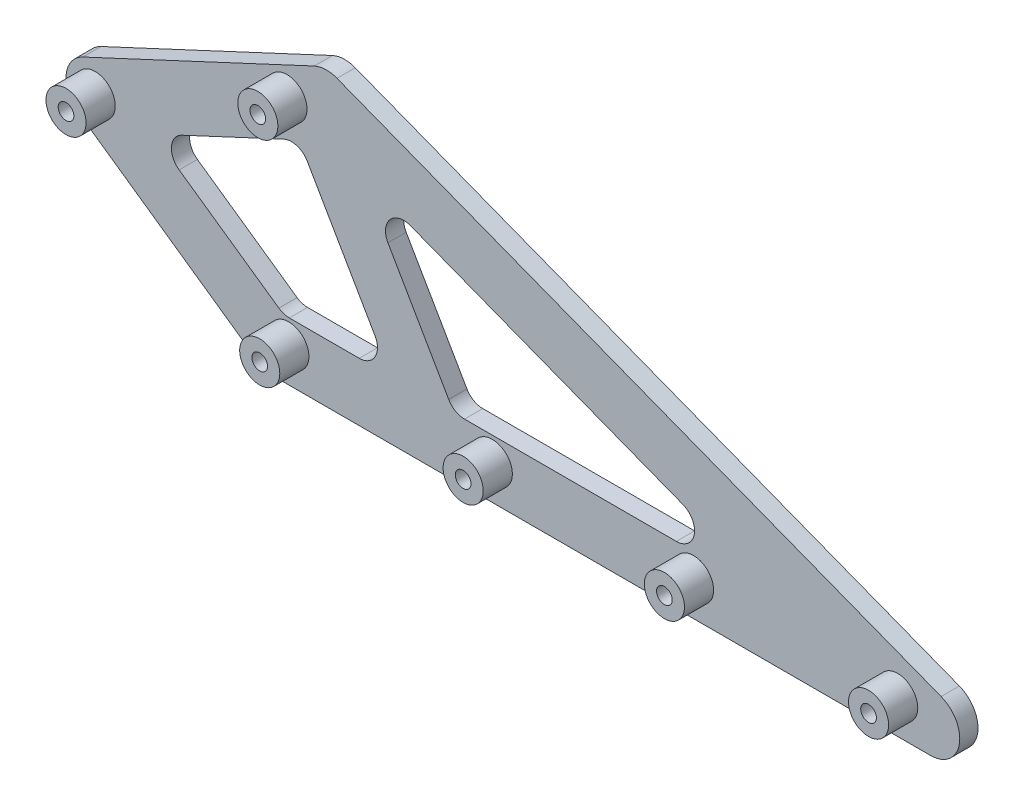
SolidWorks part; units mm, degrees
ref_plane "Front" through (0, 0, 0) normal (0, 0, 1) x (1, 0, 0)
ref_plane "Top" through (0, 0, 0) normal (0, 1, 0) x (1, 0, 0)
ref_plane "Right" through (0, 0, 0) normal (1, 0, 0) x (0, 0, -1)
sketch "Sketch1" plane through (0, 0, 0) normal (0, 0, 1) x (1, 0, 0)
  line L0 (0, 0) -> (180, 0) construction
  line L1 (0, 8) -> (180, 8)
  line L2 (0, -8) -> (180, -8)
  line L3 (0, 0) -> (-49.1491, 34.4146) construction
  line L4 (-4.5886, -6.5532) -> (-53.7377, 27.8614)
  line L5 (4.5886, 6.5532) -> (-44.5605, 40.9678)
  line L6 (-49.1491, 34.4146) -> (14.2924, 63.9979) construction
  line L7 (-52.5301, 41.665) -> (10.9115, 71.2483)
  line L8 (-45.7682, 27.1641) -> (17.6734, 56.7474)
  line L9 (14.2924, 63.9979) -> (180, 0) construction
  line L10 (17.1746, 71.4606) -> (182.8822, 7.4628)
  line L11 (11.4102, 56.5351) -> (177.1178, -7.4628)
  arc A0 (0, 8) -> (0, -8) centre (0, 0) ccw
  arc A1 (180, -8) -> (180, 8) centre (180, 0) ccw
  arc A2 (-4.5886, -6.5532) -> (4.5886, 6.5532) centre (0, 0) ccw
  arc A3 (-44.5605, 40.9678) -> (-53.7377, 27.8614) centre (-49.1491, 34.4146) ccw
  arc A4 (-52.5301, 41.665) -> (-45.7682, 27.1641) centre (-49.1491, 34.4146) ccw
  arc A5 (17.6734, 56.7474) -> (10.9115, 71.2483) centre (14.2924, 63.9979) ccw
  arc A6 (17.1746, 71.4606) -> (11.4102, 56.5351) centre (14.2924, 63.9979) ccw
  arc A7 (177.1178, -7.4628) -> (182.8822, 7.4628) centre (180, 0) ccw
  point P3 (90, 0)
  point P10 (-24.5746, 17.2073)
  point P17 (-17.4284, 49.2062)
  point P24 (97.1462, 31.9989)
  dimension "D2" = 8
  dimension "D1" = 180
  dimension "D3" = 60
  dimension "D4" = 35
  dimension "D5" = 70
  dimension "D6" = 25
extrude "Boss-Extrude1" add sketch "Sketch1" along normal blind 5 contours A6 L7 A3 L5 L8 L11 | A5 L8 L11 L1 A1 L10 | A7 L11 L1 L5 A2 L2 | A4 L4 A0 L1 L5 L8 | L11 A7 A1 L1 | A5 A6 L11 L8 | A3 A4 L8 L5 | A0 A2 L5 L1
sketch "Sketch2" plane through (0, 0, 5) normal (0, 0, 1) x (1, 0, 0)
  line L0 (-33.21, 33.0201) -> (14.587, 55.3082) construction
  line L1 (2.5224, 8) -> (-33.21, 33.0201) construction
  line L2 (2.5224, 8) -> (137.0806, 8) construction
  line L3 (14.587, 55.3082) -> (137.0806, 8) construction
  line L4 (-33.21, 33.0201) -> (14.587, 55.3082)
  line L5 (2.5224, 8) -> (-33.21, 33.0201)
  line L6 (2.5224, 8) -> (137.0806, 8)
  line L7 (14.587, 55.3082) -> (137.0806, 8)
  line L8 (6.7404, 51.6493) -> (31.9413, 8)
  line L9 (24.0609, 51.6493) -> (49.2618, 8)
  line M15 (14.587, 55.3082) -> (137.0806, 8)
  dimension "D1" = 60
  dimension "D2" = 15
extrude "Boss-Extrude2" add sketch "Sketch2" against normal through all contours L9 L4 L8 L6 M15
fillet "Fillet1" radius 5 7 edges at (137.0806, 8, 2.5) (24.0609, 51.6493, 2.5) (49.2618, 8, 2.5) (31.9413, 8, 2.5) (2.5224, 8, 2.5) (-33.21, 33.0201, 2.5) (6.7404, 51.6493, 2.5)
sketch "Sketch3" plane through (0, 0, 5) normal (0, 0, 1) x (1, 0, 0)
  line L0 (-49.1491, 34.4146) -> (3.9817, 1.5) construction
  line L1 (-4.5886, -6.5532) -> (-53.7377, 27.8614) construction
  line L2 (-4.5886, -6.5532) -> (-53.7377, 27.8614)
  line L3 (3.9817, 1.5) -> (59.7817, 1.5) construction
  line L4 (59.7817, 1.5) -> (114.9817, 1.5) construction
  line L5 (0, -8) -> (180, -8) construction
  line L6 (0, -8) -> (180, -8)
  line L7 (114.9817, 1.5) -> (170.9817, 1.5) construction
  line L8 (-49.1491, 34.4146) -> (3.4592, 60) construction
  line L9 (-52.5301, 41.665) -> (10.9115, 71.2483) construction
  line L10 (-52.5301, 41.665) -> (10.9115, 71.2483)
  arc A0 (-52.5301, 41.665) -> (-53.7377, 27.8614) centre (-49.1491, 34.4146) ccw construction
  arc A1 (-52.5301, 41.665) -> (-53.7377, 27.8614) centre (-49.1491, 34.4146) ccw
  circle A2 centre (-49.1491, 34.4146) radius 2.15
  circle A3 centre (-49.1491, 34.4146) radius 5.5
  circle A4 centre (3.9817, 1.5) radius 5.5
  circle A5 centre (3.9817, 1.5) radius 2.15
  circle A6 centre (59.7817, 1.5) radius 2.15
  circle A7 centre (59.7817, 1.5) radius 5.5
  circle A8 centre (114.9817, 1.5) radius 2.15
  circle A9 centre (114.9817, 1.5) radius 5.5
  circle A10 centre (170.9817, 1.5) radius 2.15
  circle A11 centre (170.9817, 1.5) radius 5.5
  circle A12 centre (3.4592, 60) radius 5.5
  circle A13 centre (3.4592, 60) radius 2.15
  dimension "D1" = 11
  dimension "D2" = 4.3
  dimension "D3" = 62.5
  dimension "D4" = 55.8
  dimension "D5" = 111
  dimension "D6" = 167
  dimension "D7" = 58.5
  dimension "D8" = 9.5
  dimension "D9" = 68
extrude "Boss-Extrude3" add sketch "Sketch3" along normal blind 8 contours A3 A2 | A4 | A7 | A9 | A11 | A5 | A6 | A8 | A10 | A12 | A13
sketch "Sketch4" plane through (0, 0, 5) normal (0, 0, 1) x (1, 0, 0)
  circle A0 centre (-49.1491, 34.4146) radius 2.15 construction
  circle A1 centre (-49.1491, 34.4146) radius 2.15
  circle A2 centre (3.9817, 1.5) radius 2.15 construction
  circle A3 centre (3.9817, 1.5) radius 2.15
  circle A4 centre (59.7817, 1.5) radius 2.15 construction
  circle A5 centre (59.7817, 1.5) radius 2.15
  circle A6 centre (114.9817, 1.5) radius 2.15 construction
  circle A7 centre (114.9817, 1.5) radius 2.15
  circle A8 centre (170.9817, 1.5) radius 2.15 construction
  circle A9 centre (170.9817, 1.5) radius 2.15
  circle A10 centre (3.4592, 60) radius 2.15 construction
  circle A11 centre (3.4592, 60) radius 2.15
extrude "Cut-Extrude1" cut sketch "Sketch4" against normal through all
sketch "Sketch5" plane through (0, 0, 0) normal (0, 0, -1) x (-1, 0, 0)
  circle A0 centre (-114.9817, 1.5) radius 2.15 construction
  circle A1 centre (-59.7817, 1.5) radius 2.15 construction
  circle A2 centre (-3.9817, 1.5) radius 2.15 construction
  circle A3 centre (49.1491, 34.4146) radius 2.15 construction
  circle A4 centre (-3.4592, 60) radius 2.15 construction
  circle A5 centre (-114.9817, 1.5) radius 2.15
  circle A6 centre (-59.7817, 1.5) radius 2.15
  circle A7 centre (-3.9817, 1.5) radius 2.15
  circle A8 centre (49.1491, 34.4146) radius 2.15
  circle A9 centre (-3.4592, 60) radius 2.15
  circle A10 centre (-170.9817, 1.5) radius 2.15 construction
  circle A11 centre (-170.9817, 1.5) radius 2.15
  circle A12 centre (-3.4592, 60) radius 4
  circle A13 centre (49.1491, 34.4146) radius 4
  circle A14 centre (-3.9817, 1.5) radius 4
  circle A15 centre (-59.7817, 1.5) radius 4
  circle A16 centre (-114.9817, 1.5) radius 4
  circle A17 centre (-170.9817, 1.5) radius 4
  dimension "D1" = 8
extrude "Cut-Extrude2" [suppressed] cut sketch "Sketch5" against normal blind 2
fillet "Fillet2" [suppressed] radius 1
